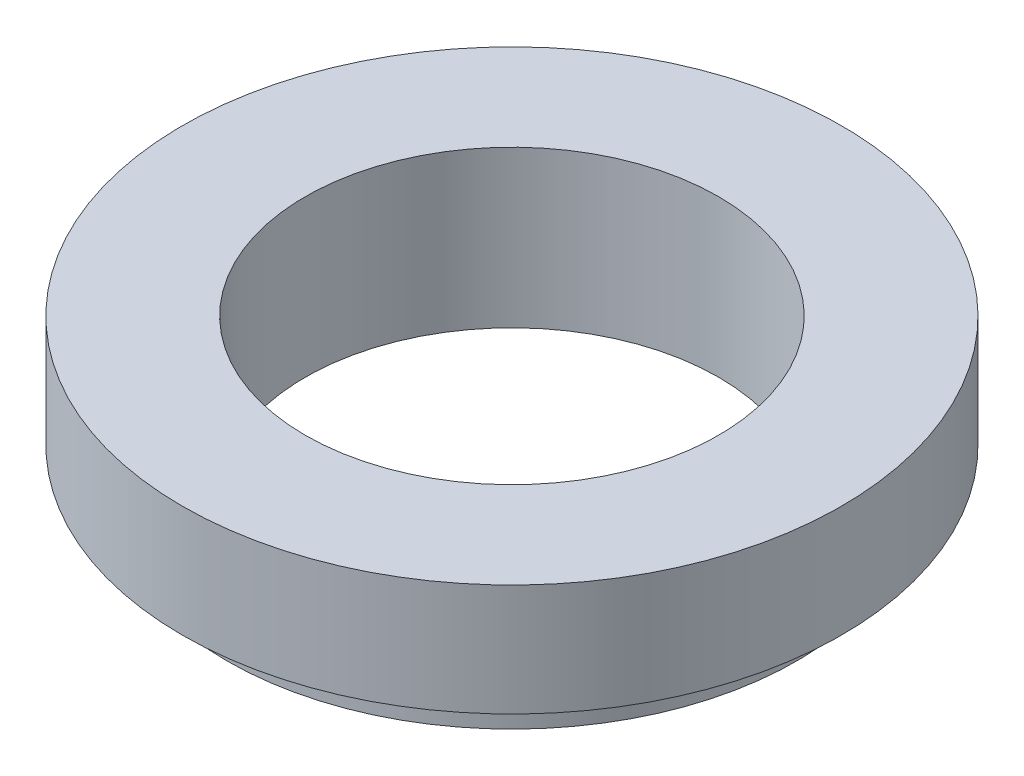
SolidWorks part; units mm, degrees
material "Бронза"
ref_plane "Спереди" through (0, 0, 0) normal (0, 0, 1) x (1, 0, 0)
ref_plane "Сверху" through (0, 0, 0) normal (0, 1, 0) x (1, 0, 0)
ref_plane "Справа" through (0, 0, 0) normal (1, 0, 0) x (0, 0, -1)
sketch "Эскиз1" plane through (0, 0, 0) normal (0, 0, 1) x (1, 0, 0)
  line L0 (0, 0) -> (0, -30.1882) construction
  line L1 (18.5, 0) -> (18.5, -14)
  line L2 (18.5, -14) -> (25.5, -14)
  line L3 (25.5, -14) -> (25.5, -10)
  line L4 (25.5, -10) -> (29.5, -10)
  line L5 (29.5, -10) -> (29.5, 0)
  line L6 (29.5, 0) -> (18.5, 0)
  dimension "D1" = 11
  dimension "D2" = 14
  dimension "D3" = 10
  dimension "D4" = 59
  dimension "D5" = 7
revolve "Повернуть1" add sketch "Эскиз1" angle 360 about L0
